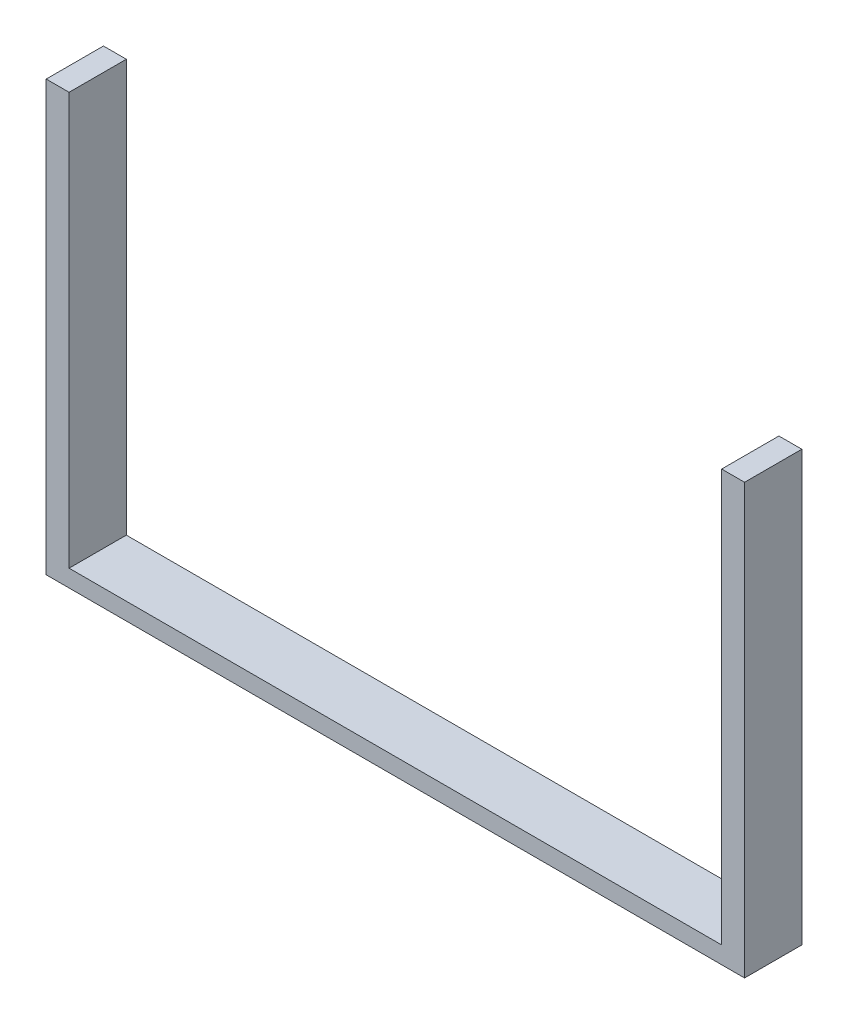
SolidWorks part; units mm, degrees
ref_plane "Front Plane" through (0, 0, 0) normal (0, 0, 1) x (1, 0, 0)
ref_plane "Top Plane" through (0, 0, 0) normal (0, 1, 0) x (1, 0, 0)
ref_plane "Right Plane" through (0, 0, 0) normal (1, 0, 0) x (0, 0, -1)
sketch "Sketch1" plane through (0, 0, 0) normal (0, 0, 1) x (1, 0, 0)
  line L0 (0, 0) -> (0, 77.5353) construction
  line L1 (-61, 75) -> (-61, 0)
  line L2 (61, 75) -> (61, 0)
  line L3 (-61, 75) -> (-57, 75)
  line L4 (-57, 75) -> (-57, 0)
  line L5 (-57, 0) -> (-61, 0)
  line L6 (57, 0) -> (61, 0)
  line L7 (57, 75) -> (57, 0)
  line L8 (61, 75) -> (57, 75)
  dimension "D1" = 122
  dimension "D2" = 4
  dimension "D3" = 75
extrude "Boss-Extrude1" add sketch "Sketch1" along normal blind 10
sketch "Sketch3" plane through (0, 0, 0) normal (0, 0, 1) x (1, 0, 0)
  line L0 (61, 0) -> (61, 75) construction
  line L1 (-61, 0) -> (61, 0)
  line L2 (-61, 0) -> (-61, 3)
  line L3 (-61, 3) -> (61, 3)
  line L4 (61, 0) -> (61, 3)
  dimension "D1" = 3
extrude "Boss-Extrude2" add sketch "Sketch3" along normal up to surface (10 mm away) up to face at (-59, 37.5, 10)
